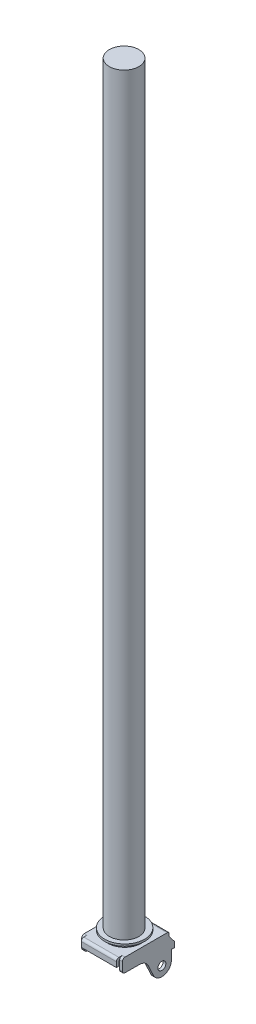
SolidWorks part; units mm, degrees
ref_plane "Front Plane" through (0, 0, 0) normal (0, 0, 1) x (1, 0, 0)
ref_plane "Top Plane" through (0, 0, 0) normal (0, 1, 0) x (1, 0, 0)
ref_plane "Right Plane" through (0, 0, 0) normal (1, 0, 0) x (0, 0, -1)
sketch "Sketch1" plane through (0, 0, 0) normal (0, 1, 0) x (1, 0, 0)
  line L1 (-17.6212, -22.5425) -> (17.6212, -22.5425)
  line L2 (-17.6212, -22.5425) -> (-17.6212, 22.5425)
  line L3 (-17.6212, 22.5425) -> (17.6212, 22.5425)
  line L4 (17.6212, -22.5425) -> (17.6212, 22.5425)
  line L5 (-17.6212, -22.5425) -> (17.6212, 22.5425) construction
  line L6 (-17.6212, 22.5425) -> (17.6212, -22.5425) construction
  point P0 (0, 0)
  dimension "D1" = 35.2425
  dimension "D2" = 45.085
extrude "Boss-Extrude1" add sketch "Sketch1" along normal blind 2.794
sketch "Sketch3" plane through (0, 0, 22.5425) normal (0, 0, 1) x (1, 0, 0)
  line L0 (-17.6212, 2.794) -> (17.6212, 2.794)
  line L1 (-17.6212, 2.794) -> (-17.6212, -4.826)
  line L2 (17.6212, 2.794) -> (17.6212, -4.826)
  line L3 (-17.6212, -4.826) -> (17.6212, -4.826)
  dimension "D1" = 7.62
extrude "Boss-Extrude2" add sketch "Sketch3" along normal blind 2.794
sketch "Sketch4" plane through (0, 0, -22.5425) normal (0, 0, -1) x (-1, 0, 0)
  line L0 (-17.6212, 2.794) -> (17.6212, 2.794)
  line L1 (-17.6212, 2.794) -> (-17.6212, -13.081)
  line L2 (17.6212, 2.794) -> (17.6212, -13.081)
  line L3 (-17.6212, -13.081) -> (17.6212, -13.081)
  dimension "D1" = 15.875
extrude "Boss-Extrude3" add sketch "Sketch4" along normal blind 2.794
sketch "Sketch5" plane through (-17.6212, 0, 0) normal (-1, 0, 0) x (0, 0, 1)
  line L0 (-24.5745, 2.794) -> (-24.5745, -0.2497)
  line L1 (-25.3365, 2.794) -> (25.3365, 2.794) construction
  line L2 (-24.5745, 2.794) -> (19.5707, 2.794)
  line L3 (22.1107, 0.254) -> (22.1107, -8.3566)
  line L4 (-25.3365, -13.081) -> (-25.3365, 2.794) construction
  line L5 (19.5707, -10.8966) -> (5.0683, -10.8966)
  line L6 (-25.0918, -1.786) -> (-30.3911, -8.763)
  line L7 (-30.3911, -8.763) -> (-30.3911, -13.843)
  line L8 (-30.3911, -13.843) -> (-26.9875, -13.843)
  line L9 (-8.8696, -27.2131) -> (-4.1881, -16.8678)
  line L10 (-26.9875, -23.3045) -> (-26.9875, -13.843)
  circle A0 centre (-17.507, -23.3045) radius 3.9942
  arc A1 (-8.8696, -27.2131) -> (-26.9875, -23.3045) centre (-17.507, -23.3045) cw
  arc A2 (22.1107, -8.3566) -> (19.5707, -10.8966) centre (19.5707, -8.3566) cw
  arc A3 (19.5707, 2.794) -> (22.1107, 0.254) centre (19.5707, 0.254) cw
  arc A4 (-24.5745, -0.2497) -> (-25.0918, -1.786) centre (-27.1145, -0.2497) cw
  arc A5 (5.0683, -10.8966) -> (-4.1881, -16.8678) centre (5.0683, -21.0566) ccw
  point P18 (22.1107, -10.8966)
  point P21 (22.1107, 2.794)
  point P24 (-24.5745, -1.1049)
  point P27 (-1.4859, -10.8966)
  dimension "D7" = 7.9883
  dimension "D9" = 5.4864
  dimension "D12" = 2.54
  dimension "D13" = 10.16
  dimension "D1" = 46.6852
  dimension "D2" = 13.6906
  dimension "D3" = 16.637
  dimension "D4" = 3.8989
  dimension "D5" = 5.08
  dimension "D6" = 52.5018
  dimension "D8" = 26.0985
  dimension "D10" = 3.4036
  dimension "D11" = 23.5966
  dimension "D14" = 0.762
extrude "Boss-Extrude5" add sketch "Sketch5" along normal blind 2.794
ref_plane "Plane1" through (0, 0, 0) normal (1, 0, 0) x (0, 0, -1)
mirror "Mirror1" about plane through (0, 0, 0) normal (1, 0, 0) of "Boss-Extrude5"
sketch "Sketch6" plane through (0, 0, 0) normal (1, 0, 0) x (0, 0, -1)
  line L0 (0.5588, 2.794) -> (17.2339, 2.794)
  line L1 (-19.5707, 2.794) -> (24.5745, 2.794) construction
  line L2 (25.3365, 2.794) -> (25.3365, -2.1081) construction
  line L3 (17.2339, 2.794) -> (17.2339, 6.1087)
  line L4 (17.2339, 6.1087) -> (20.5994, 6.1087)
  line L5 (20.5994, 6.1087) -> (20.5994, 8.1153)
  line L6 (0.5588, 2.794) -> (0.5588, 8.1153)
  line L7 (0.5588, 8.1153) -> (20.5994, 8.1153)
  dimension "D1" = 16.6751
  dimension "D2" = 8.1026
  dimension "D3" = 20.0406
  dimension "D4" = 3.3147
  dimension "D5" = 2.0066
revolve "Revolve1" add sketch "Sketch6" angle 360 about L6
sketch "Sketch8" plane through (0, 8.1153, 0) normal (0, 1, 0) x (1, 0, 0)
  circle A0 centre (0, 0) radius 14.8209
  dimension "D1" = 29.6418
extrude "Boss-Extrude6" add sketch "Sketch8" along normal blind 755.65
fillet "Fillet1" radius 2.54 2 edges at (0, 2.794, -25.3365) (0, 2.794, 25.3365)
